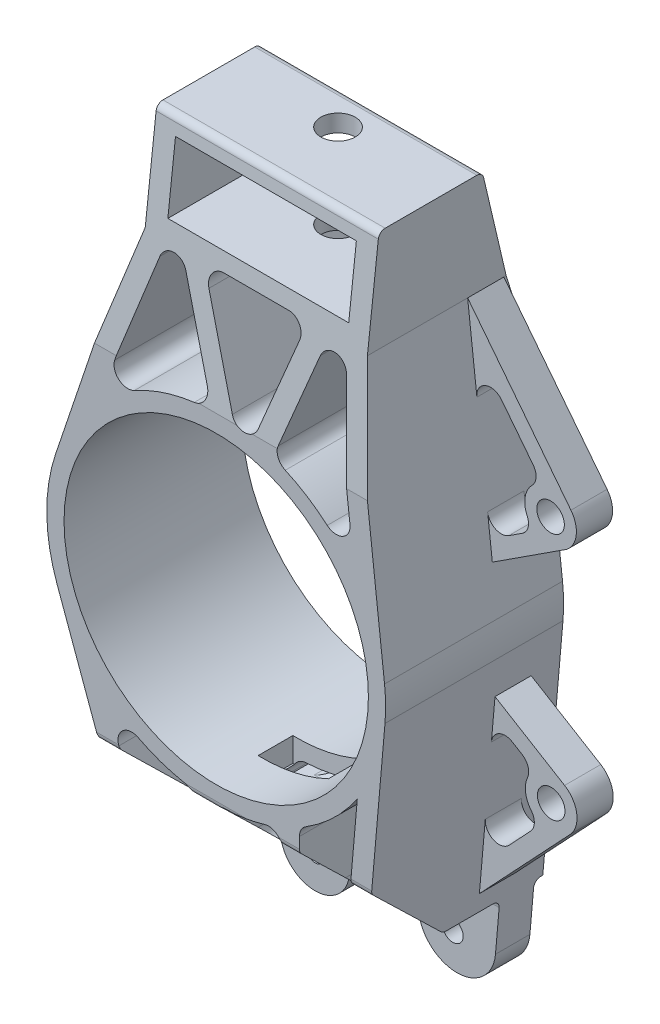
SolidWorks part; units mm, degrees
ref_plane "Front Plane" through (0, 0, 0) normal (0, 0, 1) x (1, 0, 0)
ref_plane "Top Plane" through (0, 0, 0) normal (0, 1, 0) x (1, 0, 0)
ref_plane "Right Plane" through (0, 0, 0) normal (1, 0, 0) x (0, 0, -1)
sketch "Sketch1" plane through (0, 0, 0) normal (0, 0, 1) x (1, 0, 0)
  line L0 (-24.3331, 81.8767) -> (-46.6088, 15.6856)
  line L1 (-24.3331, 111.3767) -> (40.1669, 111.3767)
  line L2 (-24.3331, 111.3767) -> (-24.3331, 81.8767)
  line L4 (40.1669, 111.3767) -> (40.1669, 81.8767)
  line L5 (40.1669, 81.8767) -> (48.8613, 5.567)
  line L7 (-1.4898, 81.8767) -> (17.3237, 81.8767)
  line L8 (-18.3331, 106.3767) -> (34.1669, 106.3767)
  line L9 (-18.3331, 106.3767) -> (-18.3331, 86.8767)
  line L10 (-18.3331, 86.8767) -> (34.1669, 86.8767)
  line L11 (34.1669, 106.3767) -> (34.1669, 86.8767)
  line L20 (-24.3331, 81.8767) -> (40.1669, 81.8767) construction
  line L23 (-94.694, 0) -> (182.7969, 0) construction
  line L24 (41.8901, -85.4419) -> (48.9903, -4.2861)
  line L25 (-19.916, -89.0664) -> (-46.2117, -16.8197)
  line L26 (0, -49.1774) -> (0, -71.1774) construction
  line L27 (-26.4271, -71.1774) -> (43.1381, -71.1774) construction
  line L28 (-17.5098, -95.6774) -> (40.9946, -95.6774) construction
  line L29 (-5.2265, 76.4496) -> (4.4727, 51.0532)
  line L30 (11.9744, 51.1292) -> (21.0886, 76.5256)
  line L31 (34.9275, 74.8611) -> (38.8293, 40.6146)
  line L32 (27.1883, 75.7594) -> (17.9116, 49.9101)
  line L33 (-12.0228, 77.4277) -> (-3.136, 54.1586)
  line L34 (-19.5506, 77.2764) -> (-29.4531, 47.8516)
  line L35 (-0.4271, -71.1774) -> (19.5729, -71.1774)
  line L36 (-28.2752, -48.5569) -> (-22.8198, -63.5455)
  line L37 (-19.061, -66.1774) -> (-10.2277, -66.1774)
  line L38 (-6.2277, -62.1774) -> (-6.2277, -52.1846)
  line L39 (24.1566, -45.1115) -> (24.1566, -62.1774)
  line L40 (28.1566, -66.1774) -> (37.5526, -66.1774)
  line L41 (37.5526, -66.1774) -> (40.9615, -27.2135)
  line L42 (-1.2277, -53.1051) -> (-1.2277, -62.1774)
  line L43 (2.7723, -66.1774) -> (15.1566, -66.1774)
  line L44 (19.1566, -62.1774) -> (19.1566, -50.9717)
  line L45 (-26.4271, -71.1774) -> (43.1381, -71.1774) construction
  line L46 (-0.4271, -71.1774) -> (-0.4271, -85.6774)
  line L47 (19.5729, -71.1774) -> (19.5729, -85.6774)
  line L48 (-10.4745, -85.6299) -> (55.2781, -85.6299) construction
  line L49 (0, 0) -> (0, -266.4589) construction
  line L50 (0, -266.4589) -> (0, 244.2731) construction
  arc A3 (-46.6088, 15.6856) -> (-46.2117, -16.8197) centre (0, 0) ccw
  arc A6 (-32.5224, -36.8879) -> (-6.2277, -48.7815) centre (0, 0) ccw construction
  arc A7 (34.9275, 74.8611) -> (27.1883, 75.7594) centre (30.9532, 74.4083) ccw
  arc A8 (-12.0228, 77.4277) -> (-19.5506, 77.2764) centre (-15.7595, 76.0005) ccw
  arc A9 (4.4727, 51.0532) -> (11.9744, 51.1292) centre (8.2095, 52.4803) ccw
  arc A10 (17.3237, 81.8767) -> (21.0886, 76.5256) centre (17.3237, 77.8767) cw
  arc A11 (-1.4898, 81.8767) -> (-5.2265, 76.4496) centre (-1.4898, 77.8767) ccw
  arc A12 (-23.7318, 43.0723) -> (-6.3557, 48.765) centre (0, 0) cw
  arc A13 (20.046, 44.9064) -> (32.2333, 37.1408) centre (0, 0) cw
  arc A14 (38.8293, 40.6146) -> (32.2333, 37.1408) centre (34.8551, 40.1617) cw
  arc A15 (17.9116, 49.9101) -> (20.046, 44.9064) centre (21.6765, 48.559) ccw
  arc A16 (-3.136, 54.1586) -> (-6.3557, 48.765) centre (-6.8727, 52.7315) cw
  arc A17 (-29.4531, 47.8516) -> (-23.7318, 43.0723) centre (-25.662, 46.5757) ccw
  arc A18 (-22.6723, -43.6393) -> (-9.4584, -48.2593) centre (0, 0) ccw
  arc A19 (-1.2277, -49.1621) -> (19.1566, -45.2929) centre (0, 0) ccw construction
  arc A20 (2.5637, -49.1106) -> (14.0165, -47.1376) centre (0, 0) ccw
  arc A21 (24.1566, -42.8355) -> (40.9615, -27.2135) centre (0, 0) ccw construction
  arc A22 (26.0387, -41.7182) -> (40.9615, -27.2135) centre (0, 0) ccw
  arc A23 (48.9903, -4.2861) -> (-46.2117, -16.8197) centre (0, 0) ccw construction
  arc A24 (48.9903, -4.2861) -> (48.8613, 5.567) centre (0, 0) ccw
  arc A25 (-1.2277, -62.1774) -> (2.7723, -66.1774) centre (2.7723, -62.1774) ccw
  arc A26 (15.1566, -66.1774) -> (19.1566, -62.1774) centre (15.1566, -62.1774) ccw
  arc A27 (19.1566, -50.9717) -> (14.0165, -47.1376) centre (15.1566, -50.9717) ccw
  arc A28 (-1.2277, -53.1051) -> (2.5637, -49.1106) centre (2.7723, -53.1051) cw
  arc A29 (-6.2277, -52.1846) -> (-9.4584, -48.2593) centre (-10.2277, -52.1846) ccw
  arc A30 (-10.2277, -66.1774) -> (-6.2277, -62.1774) centre (-10.2277, -62.1774) ccw
  arc A31 (-22.8198, -63.5455) -> (-19.061, -66.1774) centre (-19.061, -62.1774) ccw
  arc A32 (-28.2752, -48.5569) -> (-22.6723, -43.6393) centre (-24.5164, -47.1888) cw
  arc A33 (24.1566, -62.1774) -> (28.1566, -66.1774) centre (28.1566, -62.1774) ccw
  arc A34 (24.1566, -45.1115) -> (26.0387, -41.7182) centre (28.1566, -45.1115) cw
  arc A35 (-0.4271, -85.6774) -> (-19.916, -89.0664) centre (-10.4745, -85.6299) cw
  arc A36 (19.5729, -85.6774) -> (41.8901, -85.4419) centre (30.72, -84.4646) ccw
  circle A37 centre (-10.4745, -85.6299) radius 3
  circle A38 centre (29.5255, -85.6299) radius 3
  circle A39 centre (0, 0) radius 44.1774
  point P1 (24.1566, -53.6445)
  point P46 (40.2351, 28.2765)
  point P49 (16.6113, 46.287)
  point P52 (-1.2277, 49.1621)
  point P55 (-33.4139, 36.0823)
  point P65 (7.9169, 81.8767)
  point P66 (7.9169, 106.3767)
  point P85 (8.25, 48.4805)
  point P100 (-0.4271, -71.1774)
  point P101 (19.5729, -71.1774)
  dimension "D14" = 98.3549
  dimension "D12" = 98.3549
  dimension "D13" = 24.5
  dimension "D15" = 4
  dimension "D16" = 4
  dimension "D28" = 4
  dimension "D29" = 4
  dimension "D32" = 69.5652
  dimension "D33" = 26
  dimension "D35" = 6
  dimension "D36" = 40
  dimension "D37" = 5
  dimension "D2" = 64.5
  dimension "D3" = 96.5
  dimension "D4" = 29.5
  dimension "D5" = 108.6
  dimension "D6" = 5
  dimension "D7" = 5
  dimension "D8" = 6
  dimension "D9" = 6
  dimension "D10" = 85
  dimension "D11" = 70
  dimension "D17" = 22
  dimension "D18" = 6
  dimension "D19" = 6
  dimension "D20" = 6
  dimension "D21" = 6
  dimension "D22" = 4.4727
  dimension "D23" = 5
  dimension "D24" = 6
  dimension "D25" = 6
  dimension "D26" = 5
  dimension "D27" = 5
  dimension "D30" = 19.1566
  dimension "D31" = 10
  dimension "D34" = 20
extrude "Boss-Extrude1" add sketch "Sketch1" along normal mid plane 51.67
sketch "Sketch3" plane through (0, 0, 0) normal (1, 0, 0) x (0, 0, -1)
  line L0 (25.835, -95.6774) -> (25.835, -71.1774)
  line L2 (25.835, -71.1774) -> (25.335, -71.1774)
  line L3 (23.335, -73.1774) -> (23.335, -95.6774)
  line L4 (-25.835, -95.6774) -> (25.835, -95.6774) construction
  line L5 (23.335, -95.6774) -> (25.835, -95.6774)
  line L6 (13.335, -95.6774) -> (13.335, -73.1774)
  line L7 (11.335, -71.1774) -> (-2.3541, -71.1774)
  line L8 (-3.7469, -70.6127) -> (-25.835, -49.1774)
  line L9 (-25.835, 49.1774) -> (-18.9504, 109.6031)
  line L10 (-25.835, 5.567) -> (-25.835, 81.8767) construction
  line L11 (0, 49.1774) -> (0, -16.8197) construction
  line L12 (0, 49.1774) -> (0, -16.8197)
  line L13 (-3.165, -71.1774) -> (-3.165, -49.1774) construction
  line L14 (-25.835, -85.4419) -> (-25.835, -4.2861) construction
  line L15 (-25.835, -49.1774) -> (-25.835, -95.6774)
  line L16 (-25.835, -95.6774) -> (13.335, -95.6774)
  line L17 (-25.835, 111.3767) -> (25.835, 111.3767) construction
  line L19 (11.6136, 109.8333) -> (25.835, 49.1774)
  line L20 (25.835, 5.567) -> (25.835, 81.8767) construction
  line L21 (-25.835, 49.1774) -> (55.9748, 49.1774) construction
  line L22 (55.9748, 49.1774) -> (-136.4579, 49.1774) construction
  line L23 (-25.835, 49.1774) -> (-25.835, 111.3767)
  line L24 (-25.835, 111.3767) -> (-16.9632, 111.3767)
  line L25 (9.6664, 111.3767) -> (25.835, 111.3767)
  line L26 (25.835, 111.3767) -> (25.835, 49.1774)
  arc A0 (25.335, -71.1774) -> (23.335, -73.1774) centre (25.335, -73.1774) ccw
  arc A1 (-18.9504, 109.6031) -> (-16.9632, 111.3767) centre (-16.9632, 109.3767) cw
  arc A2 (9.6664, 111.3767) -> (11.6136, 109.8333) centre (9.6664, 109.3767) cw
  arc A3 (13.335, -73.1774) -> (11.335, -71.1774) centre (11.335, -73.1774) ccw
  arc A4 (-2.3541, -71.1774) -> (-3.7469, -70.6127) centre (-2.3541, -69.1774) cw
  point P11 (13.335, -95.6774)
  point P30 (-20.3336, 111.3767)
  point P49 (13.335, -71.1774)
  dimension "D2" = 2
  dimension "D10" = 2
  dimension "D11" = 2
  dimension "D15" = 2
  dimension "D16" = 2
  dimension "D1" = 24.5
  dimension "D3" = 2.5
  dimension "D4" = 71.1774
  dimension "D5" = 10
  dimension "D6" = 16.5
  dimension "D7" = 22
  dimension "D8" = 6.5
  dimension "D9" = 30
  dimension "D12" = 11.6136
  dimension "D13" = 109.8333
  dimension "D14" = 9.6664
extrude "Cut-Extrude1" cut sketch "Sketch3" against normal through all both and the other way through all contours L15 L16 L6 L7 L8 | L9 A1 L24 L23 | L19 L26 L25 A2 | L0 L2 A0 L3 L5
fillet "Fillet1" radius 2 4 edges at (-31.2419, -49.1774, 25.835) (-2.7875, -49.1774, 25.835) (21.4441, -49.1774, 25.835) (42.0514, -49.1774, 25.835)
ref_plane "Plane1" through (0, 0, -6.985) normal (0, 0, 1) x (1, 0, 0)
sketch "Sketch5" plane through (0, 0, -6.985) normal (0, 0, 1) x (1, 0, 0)
  line L0 (40.1669, 81.8767) -> (70.1477, 43.5031)
  line L2 (48.8613, 5.567) -> (43.8925, 49.1774) construction
  line L3 (40.1669, 81.8767) -> (-107.5108, 81.8767) construction
  line L4 (47.3282, 19.0234) -> (69.0309, 33.1173)
  line L5 (49.9821, 61.1925) -> (59.188, 49.4095)
  line L6 (52.1168, 28.095) -> (56.0146, 30.6262)
  line L8 (42.8558, 58.2771) -> (40.1669, 81.8767)
  line L9 (47.3282, 19.0234) -> (45.964, 30.9968)
  line L10 (64.2376, 38.8857) -> (64.2376, -92.1903) construction
  line L11 (48.1076, -14.3753) -> (68.3061, -26.608)
  line L12 (45.1368, -48.3314) -> (48.9903, -4.2861) construction
  line L13 (43.5755, -66.1774) -> (69.8882, -38.1573)
  line L14 (45.0113, -49.7667) -> (43.1875, -70.6127) construction
  line L16 (8.9644, -66.1774) -> (144.1384, -66.1774) construction
  line L17 (15.1566, -66.1774) -> (2.7723, -66.1774) construction
  line L19 (53.1187, -23.2556) -> (55.9633, -24.9784)
  line L20 (52.1876, -49.7024) -> (58.4383, -43.0461)
  line L22 (47.0619, -26.3285) -> (48.1076, -14.3753)
  line L23 (45.287, -46.6156) -> (43.5755, -66.1774)
  arc A0 (70.1477, 43.5031) -> (69.0309, 33.1173) centre (64.2376, 38.8857) cw
  circle A1 centre (64.2376, 38.8857) radius 4
  circle A2 centre (64.2376, 38.8857) radius 7.5 construction
  arc A3 (58.8887, 44.143) -> (57.454, 35.6869) centre (64.2376, 38.8857) ccw
  arc A4 (49.9821, 61.1925) -> (42.8558, 58.2771) centre (46.8301, 58.7299) ccw
  arc A5 (52.1168, 28.095) -> (45.964, 30.9968) centre (49.9383, 31.4496) cw
  arc A6 (56.0146, 30.6262) -> (57.454, 35.6869) centre (53.836, 33.9809) ccw
  arc A7 (59.188, 49.4095) -> (58.8887, 44.143) centre (56.036, 46.9469) cw
  arc A8 (69.8882, -38.1573) -> (68.3061, -26.608) centre (64.4209, -33.0232) ccw
  circle A9 centre (64.4209, -33.0232) radius 4
  circle A10 centre (64.4209, -33.0232) radius 7.5 construction
  arc A11 (57.5537, -30.008) -> (58.6176, -37.7741) centre (64.4209, -33.0232) ccw
  arc A12 (52.1876, -49.7024) -> (45.287, -46.6156) centre (49.2717, -46.9642) cw
  arc A13 (58.4383, -43.0461) -> (58.6176, -37.7741) centre (55.5224, -40.3079) ccw
  arc A14 (55.9633, -24.9784) -> (57.5537, -30.008) centre (53.8912, -28.3998) cw
  arc A15 (53.1187, -23.2556) -> (47.0619, -26.3285) centre (51.0466, -26.6771) ccw
  point P25 (59.6257, 32.9713)
  point P28 (61.8542, 45.9969)
  point P53 (61.4029, -39.8892)
  point P56 (59.6676, -27.2218)
  point P59 (0, 0)
  point P60 (0, 0)
  dimension "D3" = 7.5
  dimension "D5" = 8
  dimension "D9" = 4
  dimension "D13" = 7.5
  dimension "D14" = 8
  dimension "D17" = 4
  dimension "D1" = 63.26
  dimension "D2" = 128
  dimension "D4" = 33
  dimension "D6" = 64.2376
  dimension "D7" = 5
  dimension "D8" = 5
  dimension "D10" = 133.2
  dimension "D11" = 52
  dimension "D12" = 31.2
  dimension "D15" = 5
  dimension "D16" = 5
extrude "Boss-Extrude2" add sketch "Sketch5" against normal blind 10.5
ref_plane "Plane2" through (0, 0, 0.535) normal (0, 0, 1) x (1, 0, 0)
sketch "Sketch6" plane through (0, 0, 0.535) normal (0, 0, 1) x (1, 0, 0)
  line L1 (-59.1738, 10.6856) -> (-59.1738, -11.8197)
  line L3 (-46.2117, -16.8197) -> (-221.7948, -16.8197) construction
  line L4 (-46.6088, 15.6856) -> (-235.4497, 15.6856) construction
  line L5 (-59.1738, 10.6856) -> (-54.4122, 10.6856)
  line L6 (-59.1738, -11.8197) -> (-54.4122, -11.8197)
  arc A0 (-46.6088, 15.6856) -> (-46.2117, -16.8197) centre (0, 0) ccw construction
  arc A1 (-46.6088, 15.6856) -> (-46.2117, -16.8197) centre (0, 0) ccw
  arc A2 (-54.4122, -11.8197) -> (-46.2117, -16.8197) centre (-54.4122, -21.0445) cw
  arc A3 (-54.4122, 10.6856) -> (-46.6088, 15.6856) centre (-54.4122, 19.2749) ccw
  point P11 (-49.1738, -0.6008)
  dimension "D1" = 5
  dimension "D4" = 9.2249
  dimension "D2" = 5
  dimension "D3" = 10
extrude "Boss-Extrude3" add sketch "Sketch6" against normal up to surface (26.37 mm away) up to face at (30.0885, -51.6598, -25.835)
sketch "Sketch7" plane through (-59.1738, 0, 0) normal (-1, 0, 0) x (0, 0, 1)
  line L0 (-25.835, -0.567) -> (0, 0) construction
  line L1 (-25.835, -11.8197) -> (-25.835, 10.6856) construction
  line L3 (-6.985, -168.7917) -> (-6.985, 168.7917) construction
  circle A0 centre (-16.9826, -0.3727) radius 2.75
  circle A1 centre (-6.985, -0.1533) radius 2.75
  point P9 (-6.985, 0)
  point P11 (-3.4027, -0.0747)
  point P13 (-18.6636, -0.567)
  point P14 (-6.985, 0)
  point P15 (-19.037, -0.567)
  dimension "D1" = 5.5
  dimension "D2" = 10
extrude "Cut-Extrude2" cut sketch "Sketch7" against normal up to surface (9.9977 mm away)
sketch "Sketch10" plane through (0, 111.3767, 0) normal (0, 1, 0) x (1, 0, 0)
  line L0 (40.1669, 9.6664) -> (-24.3331, 9.6664) construction
  line L1 (-24.3331, 11.6136) -> (40.1669, 11.6136) construction
  circle A0 centre (7.9169, 1.6136) radius 5
  point P2 (0, 0)
  point P5 (7.9169, 9.6664)
  dimension "D1" = 10
  dimension "D2" = 10
extrude "Cut-Extrude4" cut sketch "Sketch10" against normal up to surface (29.5 mm away) up to face at (7.9169, 81.8767, 1.9705)
sketch "Sketch11" plane through (0, 0, 0) normal (1, 0, 0) x (0, 0, -1)
  line L0 (12.835, -66.1774) -> (0.0786, -66.1774)
  line L1 (-2.0106, -65.3303) -> (-8.8552, -58.6881)
  line L2 (-6.7659, -53.5352) -> (12.835, -53.5352)
  line L3 (15.835, -56.5352) -> (15.835, -63.1774)
  line L4 (11.335, -71.1774) -> (-2.3541, -71.1774) construction
  line L6 (-3.7469, -70.6127) -> (-25.2278, -49.7667) construction
  line L7 (25.835, -16.8197) -> (25.835, -71.1774) construction
  arc A0 (-8.8552, -58.6881) -> (-6.7659, -53.5352) centre (-6.7659, -56.5352) cw
  arc A1 (0.0786, -66.1774) -> (-2.0106, -65.3303) centre (0.0786, -63.1774) cw
  arc A2 (12.835, -66.1774) -> (15.835, -63.1774) centre (12.835, -63.1774) ccw
  arc A3 (12.835, -53.5352) -> (15.835, -56.5352) centre (12.835, -56.5352) cw
  point P6 (4.4905, -71.1774)
  point P11 (-16.3416, -51.4229)
  point P14 (-14.165, -53.5352)
  point P21 (15.835, -53.5352)
  dimension "D5" = 3
  dimension "D1" = 5
  dimension "D2" = 5
  dimension "D3" = 10
  dimension "D4" = 30
extrude "Cut-Extrude5" cut sketch "Sketch11" against normal through all and the other way up to vertex
sketch "Sketch12" plane through (0, 0, 0) normal (0, 1, 0) x (1, 0, 0)
  line L0 (-1.2277, -12.4391) -> (-1.2277, -2.3541)
  line L1 (-26.4271, -2.3541) -> (43.1381, -2.3541) construction
  line L2 (-1.2277, -21.7877) -> (-1.2277, 25.835) construction
  line L3 (-1.2277, -2.3541) -> (19.1566, -2.3541)
  line L4 (19.1566, -2.3541) -> (19.1566, -12.4391)
  line L5 (19.1566, -23.9861) -> (19.1566, 25.835) construction
  line L6 (-1.2277, -12.4391) -> (19.1566, -12.4391)
extrude "Cut-Extrude6" cut sketch "Sketch12" against normal offset from surface (51.1774 mm away) 20 up to face at (8.7613, -71.1774, -16.1368)
